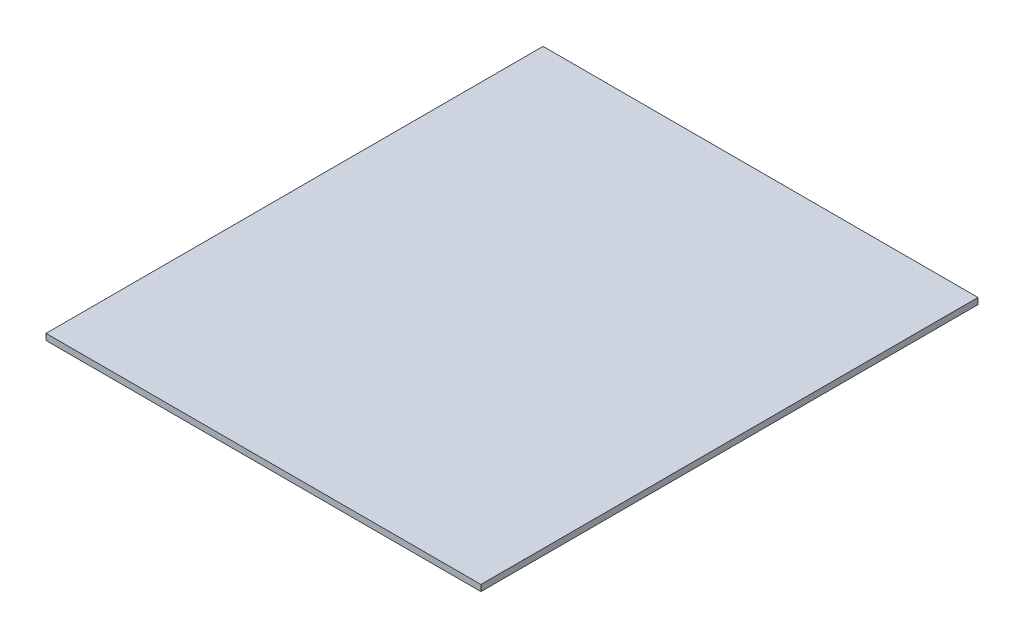
SolidWorks part; units mm, degrees
ref_plane "Front Plane" through (0, 0, 0) normal (0, 0, 1) x (1, 0, 0)
ref_plane "Top Plane" through (0, 0, 0) normal (0, 1, 0) x (1, 0, 0)
ref_plane "Right Plane" through (0, 0, 0) normal (1, 0, 0) x (0, 0, -1)
sketch "Sketch1" plane through (0, 0, 0) normal (0, 1, 0) x (1, 0, 0)
  line L0 (0, 0) -> (-35, 0)
  line L1 (-35, 0) -> (-35, -40)
  line L2 (-35, -40) -> (0, -40)
  line L3 (0, -40) -> (0, 0)
  dimension "D1" = 40
  dimension "D2" = 35
extrude "Boss-Extrude1" add sketch "Sketch1" along normal blind 0.5
scale "Scale1" scale about centroid uniform scaling yes scale factor 10
